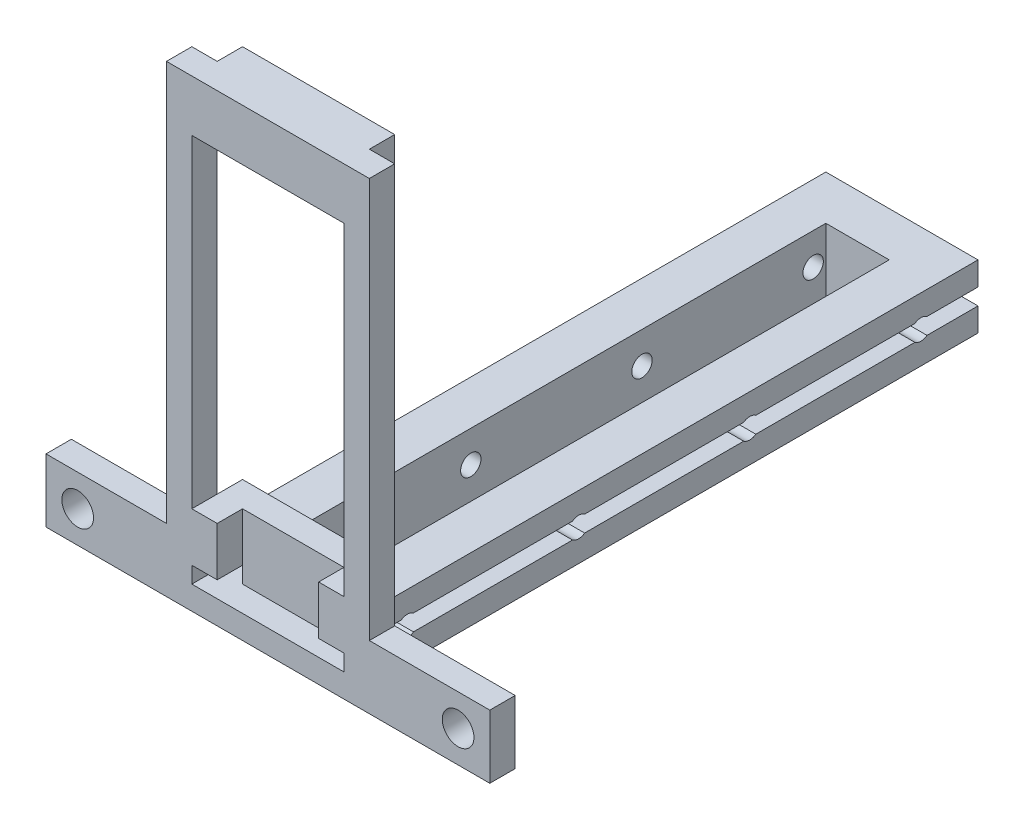
SolidWorks part; units mm, degrees
ref_plane "Front Plane" through (0, 0, 0) normal (0, 0, 1) x (1, 0, 0)
ref_plane "Top Plane" through (0, 0, 0) normal (0, 1, 0) x (1, 0, 0)
ref_plane "Right Plane" through (0, 0, 0) normal (1, 0, 0) x (0, 0, -1)
sketch "Sketch1" plane through (0, 0, 0) normal (0, 0, -1) x (1, 0, 0)
  line L1 (-44.45, -12.7) -> (44.45, -12.7)
  line L2 (-44.45, -12.7) -> (-44.45, 0)
  line L3 (-44.45, 0) -> (44.45, 0)
  line L4 (44.45, -12.7) -> (44.45, 0)
  dimension "D1" = 88.9
  dimension "D2" = 12.7
extrude "Small Base Extrude" add sketch "Sketch1" along normal blind 5.08 contours L2 L1 L4 L3
sketch "Sketch3" plane through (0, 0, -5.08) normal (0, 0, -1) x (1, 0, 0)
  line L0 (-44.45, -12.7) -> (44.45, -12.7) construction
  line L2 (-15.24, -12.7) -> (15.24, -12.7)
  line L3 (-15.24, 0) -> (15.24, 0)
  line L4 (-15.24, 0) -> (-15.24, -12.7)
  line L5 (15.24, 0) -> (15.24, -12.7)
  line L6 (0, 0) -> (0, -12.7) construction
  line L7 (15.24, -6.35) -> (-15.24, -6.35) construction
  point P10 (0, -6.35)
  dimension "D1" = 30.48
extrude "Main Tower Extrude" add sketch "Sketch3" along normal blind 121.92
sketch "Sketch4" plane through (0, 12.7, 0) normal (0, 1, 0) x (1, 0, 0)
  line L0 (-15.24, 5.08) -> (15.24, 5.08) construction
  line L1 (0, 118.11) -> (0, 127) construction
  line L2 (-6.35, 118.11) -> (6.35, 118.11)
  line L3 (-6.35, 118.11) -> (-6.35, 10.16)
  line L4 (-6.35, 10.16) -> (6.35, 10.16)
  line L5 (6.35, 118.11) -> (6.35, 10.16)
  line L7 (-15.24, 66.04) -> (-6.35, 66.04) construction
  line L8 (-15.24, 127) -> (-15.24, 5.08) construction
  line L9 (6.35, 64.135) -> (15.24, 64.135) construction
  line L10 (15.24, 127) -> (15.24, 5.08) construction
  line L12 (15.24, 127) -> (-15.24, 127) construction
  dimension "D1" = 8.89
  dimension "D2" = 5.08
extrude "Filament Channel Cut" cut sketch "Sketch4" against normal through all
sketch "Sketch6" plane through (-6.35, 0, 0) normal (1, 0, 0) x (0, 0, -1)
  line L0 (12.7, 0) -> (12.7, 12.7) construction
  line L5 (118.11, 0) -> (10.16, 0) construction
  line L8 (118.11, 12.7) -> (10.16, 12.7) construction
  line L9 (10.16, 0) -> (10.16, 12.7) construction
  circle A0 centre (12.7, 6.35) radius 2.0396
  dimension "D1" = 4.0792
  dimension "D2" = 2.54
extrude "Cut-Extrude3" cut sketch "Sketch6" against normal up to next (8.89 mm away)
pattern_linear "LPattern1" count 4 spacing 34.29 along (0, 0, -1) of "Cut-Extrude3"
sketch "Sketch9" plane through (6.35, 57.0019, -16.025) normal (-1, 0, 0) x (0, 0, 1)
  line L0 (3.325, -44.3019) -> (3.325, -57.0019) construction
  line L1 (5.865, -57.0019) -> (-102.085, -57.0019) construction
  line L2 (5.865, -44.3019) -> (-102.085, -44.3019) construction
  line L4 (5.865, -57.0019) -> (5.865, -44.3019) construction
  circle A0 centre (3.325, -50.6519) radius 2.0396
  dimension "D1" = 4.0792
  dimension "D2" = 2.54
extrude "Cut-Extrude6" cut sketch "Sketch9" against normal up to next (8.89 mm away)
pattern_linear "LPattern2" count 4 spacing 34.29 along (0, 0, -1) of "Cut-Extrude6"
sketch "Sketch10" plane through (0, 0, -127) normal (0, 0, -1) x (-1, 0, 0)
  line L0 (15.24, 0) -> (15.24, 12.7) construction
  line L1 (15.24, 4.7117) -> (10.16, 4.7117)
  line L2 (15.24, 4.7117) -> (15.24, 7.9883)
  line L3 (15.24, 7.9883) -> (10.16, 7.9883)
  line L4 (10.16, 4.7117) -> (10.16, 7.9883)
  line L5 (15.24, 12.7) -> (-15.24, 12.7) construction
  line L6 (-15.24, 12.7) -> (-15.24, 0) construction
  line L7 (-15.24, 7.9883) -> (-10.16, 7.9883)
  line L8 (-15.24, 7.9883) -> (-15.24, 4.7117)
  line L9 (-15.24, 4.7117) -> (-10.16, 4.7117)
  line L10 (-10.16, 7.9883) -> (-10.16, 4.7117)
  dimension "D1" = 3.2766
  dimension "D2" = 4.7117
  dimension "D3" = 5.08
  dimension "D4" = 5.08
  dimension "D5" = 4.7117
  dimension "D6" = 3.2766
extrude "Wire Channel Cut" cut sketch "Sketch10" against normal blind 228.6
sketch "Sketch11" plane through (0, 0, 0) normal (0, 0, 1) x (1, 0, 0)
  line L0 (15.24, 12.7) -> (44.45, 12.7) construction
  line L1 (-44.45, 12.7) -> (-15.24, 12.7) construction
  circle A1 centre (38.1, 6.35) radius 3.175
  circle A2 centre (-38.1, 6.35) radius 3.175
  dimension "D1" = 6.35
  dimension "D4" = 6.35
  dimension "D5" = 6.35
  dimension "D2" = 6.35
extrude "Mounting Bolt Hole Cuts" cut sketch "Sketch11" against normal blind 25.4
sketch "Sketch12" plane through (0, 12.7, 0) normal (0, 1, 0) x (1, 0, 0)
  line L0 (-44.45, 0) -> (44.45, 0) construction
  line L1 (-15.24, 0) -> (15.24, 0)
  line L2 (-15.24, 5.08) -> (-15.24, 10.16)
  line L3 (-15.24, 10.16) -> (15.24, 10.16)
  line L4 (15.24, 5.08) -> (15.24, 10.16)
  line L5 (15.24, 127) -> (15.24, 5.08) construction
  line L6 (-15.24, 127) -> (-15.24, 5.08) construction
  line L8 (-15.24, 5.08) -> (-20.32, 5.08)
  line L10 (-15.24, 0) -> (-20.32, 0)
  line L11 (-20.32, 5.08) -> (-20.32, 0)
  line L12 (15.24, 5.08) -> (20.32, 5.08)
  line L14 (15.24, 0) -> (20.32, 0)
  line L15 (20.32, 5.08) -> (20.32, 0)
  dimension "D1" = 0
  dimension "D2" = 10.16
  dimension "D3" = 5.08
  dimension "D4" = 5.08
extrude "Copper Board Extrude" add sketch "Sketch12" along normal blind 80.16
sketch "Sketch13" plane through (0, 0, -10.16) normal (0, 0, -1) x (-1, 0, 0)
  line L1 (15.24, 82.5526) -> (-15.24, 82.5526)
  line L2 (15.24, 82.5526) -> (15.24, 17.78)
  line L3 (15.24, 17.78) -> (-15.24, 17.78)
  line L4 (-15.24, 82.5526) -> (-15.24, 17.78)
  line L6 (-15.24, 92.86) -> (-15.24, 12.7) construction
  line L7 (6.35, 12.7) -> (15.24, 12.7) construction
  line L8 (15.24, 92.86) -> (15.24, 12.7) construction
  dimension "D1" = 0
  dimension "D2" = 0
  dimension "D3" = 5.08
extrude "Copper Board Cut" cut sketch "Sketch13" against normal blind 10.16
sketch "Sketch14" plane through (0, 0, 0) normal (0, 0, 1) x (1, 0, 0)
  line L0 (15.24, 17.78) -> (-15.24, 17.78) construction
  line L1 (-10.16, 4.7117) -> (10.16, 4.7117)
  line L2 (-10.16, 4.7117) -> (-10.16, 6.0833)
  line L4 (10.16, 4.7117) -> (10.16, 7.9883)
  line L6 (-10.16, 6.0833) -> (-10.16, 17.78)
  line L7 (-10.16, 17.78) -> (10.16, 17.78)
  line L8 (10.16, 7.9883) -> (10.16, 17.78)
extrude "Wire Escape Hole Cut" cut sketch "Sketch14" against normal blind 5.08
